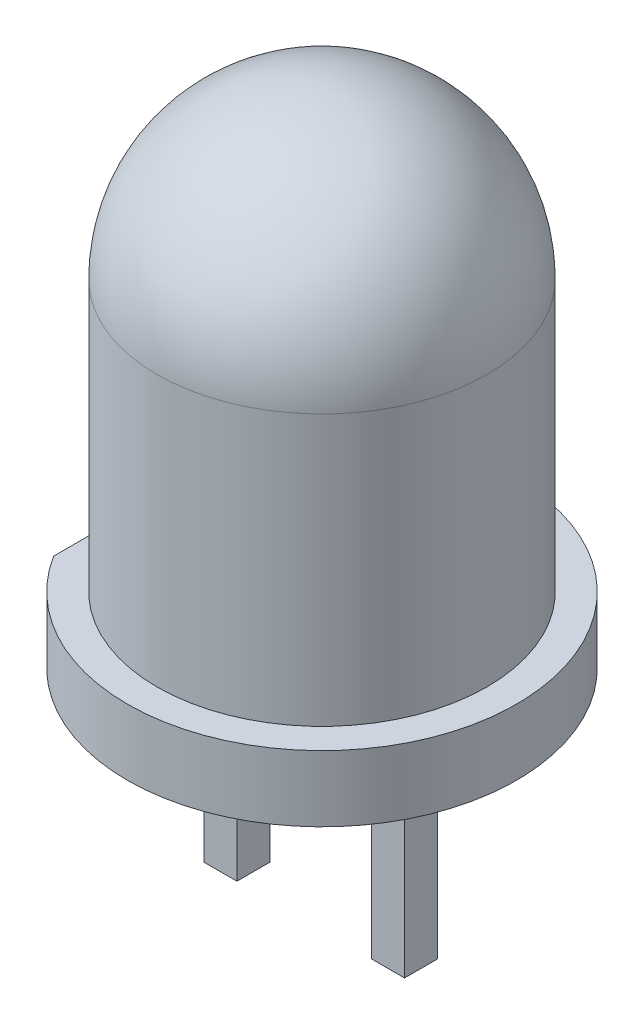
SolidWorks part; units mm, degrees
ref_plane "Alzado" through (0, 0, 0) normal (0, 0, 1) x (1, 0, 0)
ref_plane "Planta" through (0, 0, 0) normal (0, 1, 0) x (1, 0, 0)
ref_plane "Vista lateral" through (0, 0, 0) normal (1, 0, 0) x (0, 0, -1)
sketch "Croquis2" plane through (0, 0, 0) normal (1, 0, 0) x (0, 0, -1)
  line L0 (0, -1491.4716) -> (0, 1148.2312) construction
  line L1 (0, -919.5893) -> (2.95, -919.5893)
  line L2 (2.95, -919.5893) -> (2.95, -918.5893)
  line L3 (2.95, -918.5893) -> (2.5, -918.5893)
  line L4 (2.5, -918.5893) -> (2.5, -914.4893)
  line L5 (0, -919.5893) -> (0, -911.9893)
  arc A0 (2.5, -914.4893) -> (0, -911.9893) centre (0, -914.4893) ccw
  dimension "D1" = 7.6
  dimension "D2" = 1
  dimension "D3" = 2.95
  dimension "D4" = 2.5
revolve "Revolución1" add sketch "Croquis2" angle 360 about L0
sketch "Croquis3" plane through (0, -919.5893, 0) normal (0, -1, 0) x (1, 0, 0)
  line L0 (1.52, 0.2688) -> (1.52, -0.2312)
  line L1 (1.52, -0.2312) -> (1.02, -0.2312)
  line L2 (1.02, -0.2312) -> (1.02, 0.2688)
  line L3 (1.02, 0.2688) -> (1.52, 0.2688)
  line L4 (-1.02, -0.2312) -> (-1.52, -0.2312)
  line L5 (-1.52, -0.2312) -> (-1.52, 0.2688)
  line L6 (-1.52, 0.2688) -> (-1.02, 0.2688)
  line L7 (-1.02, 0.2688) -> (-1.02, -0.2312)
  circle A1 centre (0, 0) radius 2.95 construction
  dimension "D1" = 0.5
  dimension "D2" = 0.5
  dimension "D3" = 2.04
  dimension "D4" = 1.02
extrude "Saliente-Extruir3" add sketch "Croquis3" along normal blind 25.4
sketch "Croquis4" plane through (0, -918.5893, 0) normal (0, 1, 0) x (1, 0, 0)
  line L0 (-2.5, -2.5096) -> (-2.5, 3.0765)
  line L1 (-1.52, -0.2688) -> (-1.52, 0.2312) construction
  line L3 (-2.5, -2.5096) -> (-3.4125, -2.5096)
  line L4 (-3.4125, -2.5096) -> (-3.4125, 3.0765)
  line L5 (-3.4125, 3.0765) -> (-2.5, 3.0765)
  circle A0 centre (0, 0) radius 2.5 construction
extrude "Cortar-Extruir1" cut sketch "Croquis4" against normal blind 25.4
sketch "Croquis5" plane through (0, 0, 0.2688) normal (0, 0, 1) x (1, 0, 0)
  line L0 (-1.52, -943.9893) -> (-1.52, -944.9893)
  line L1 (-1.52, -944.9893) -> (-1.02, -944.9893)
  line L2 (-1.02, -944.9893) -> (-1.02, -943.9893)
  line L3 (-1.02, -943.9893) -> (-1.52, -943.9893)
  line L4 (-1.02, -944.9893) -> (-1.02, -919.5893) construction
  line L5 (-1.52, -944.9893) -> (-1.52, -919.5893) construction
  line L6 (-1.02, -944.9893) -> (-1.52, -944.9893) construction
  dimension "D1" = 1
extrude "Cortar-Extruir2" cut sketch "Croquis5" against normal up to next
sketch "Sketch1" plane through (0, 0, -0.2312) normal (0, 0, -1) x (-1, 0, 0)
  line L0 (-1.52, -944.9893) -> (-1.52, -919.5893) construction
  line L1 (1.52, -922.7643) -> (-1.52, -922.7643)
  line L2 (1.52, -922.7643) -> (1.52, -944.9893)
  line L3 (1.52, -944.9893) -> (-1.52, -944.9893)
  line L4 (-1.52, -922.7643) -> (-1.52, -944.9893)
  line L5 (1.52, -943.9893) -> (1.52, -919.5893) construction
  line L6 (-2.95, -919.5893) -> (2.5, -919.5893) construction
  dimension "D1" = 3.175
extrude "Cut-Extrude1" cut sketch "Sketch1" against normal through all
